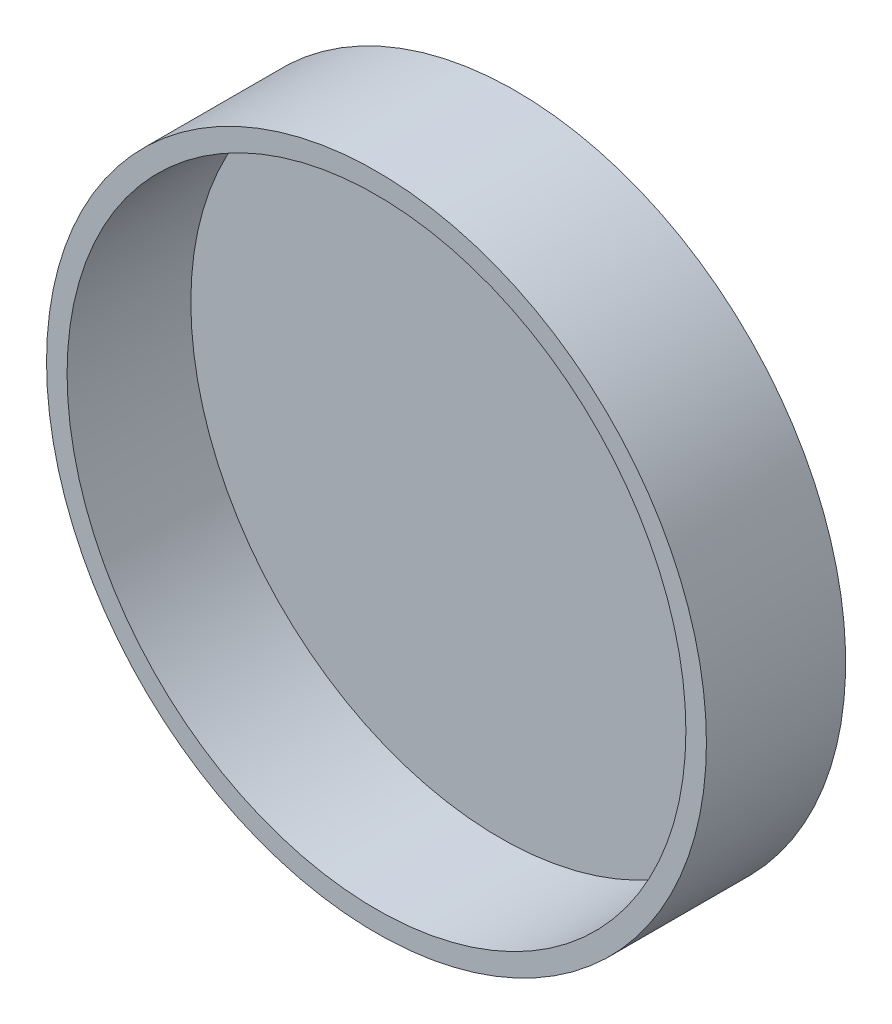
SolidWorks part; units mm, degrees
material "Plain Carbon Steel"
ref_plane "Front" through (0, 0, 0) normal (0, 0, 1) x (1, 0, 0)
ref_plane "Top" through (0, 0, 0) normal (0, 1, 0) x (1, 0, 0)
ref_plane "Right" through (0, 0, 0) normal (1, 0, 0) x (0, 0, -1)
sketch "Sketch1" plane through (0, 0, 0) normal (0, 0, 1) x (1, 0, 0)
  circle A0 centre (-33.8331, 23.9224) radius 50.8
  circle A1 centre (-33.8331, 23.9224) radius 54.1729
  dimension "D1" = 101.6
extrude "Boss-Extrude1" add sketch "Sketch1" along normal blind 20.32
sketch "Sketch2" plane through (0, 0, 0) normal (0, 0, -1) x (-1, 0, 0)
  line L0 (88.006, 23.9224) -> (-20.3398, 23.9224) construction
  circle A0 centre (33.8331, 23.9224) radius 54.1729 construction
  circle A1 centre (33.8331, 23.9224) radius 54.1729
extrude "Boss-Extrude2" add sketch "Sketch2" along normal blind 2.54
